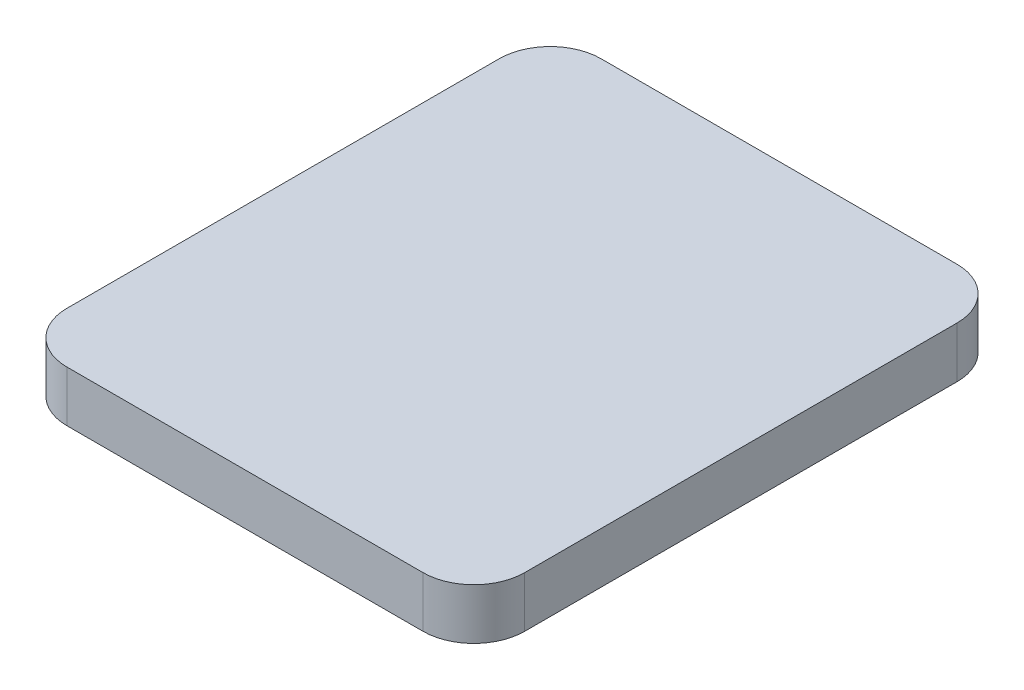
SolidWorks part; units mm, degrees
material "Custom Plastic"
ref_plane "Front Plane" through (0, 0, 0) normal (0, 0, 1) x (1, 0, 0)
ref_plane "Top Plane" through (0, 0, 0) normal (0, 1, 0) x (1, 0, 0)
ref_plane "Right Plane" through (0, 0, 0) normal (1, 0, 0) x (0, 0, -1)
sketch "Sketch1" plane through (0, 0, 0) normal (0, 1, 0) x (1, 0, 0)
  line L1 (-9, 10.5) -> (9, 10.5)
  line L2 (-9, 10.5) -> (-9, -10.5)
  line L3 (-9, -10.5) -> (9, -10.5)
  line L4 (9, 10.5) -> (9, -10.5)
  line L5 (-9, 10.5) -> (9, -10.5) construction
  line L6 (-9, -10.5) -> (9, 10.5) construction
  point P0 (0, 0)
  dimension "D1" = 21
  dimension "D2" = 18
extrude "Boss-Extrude1" add sketch "Sketch1" along normal blind 2
fillet "Fillet1" radius 2 4 edges at (-9, 1, -10.5) (9, 1, -10.5) (9, 1, 10.5) (-9, 1, 10.5)
